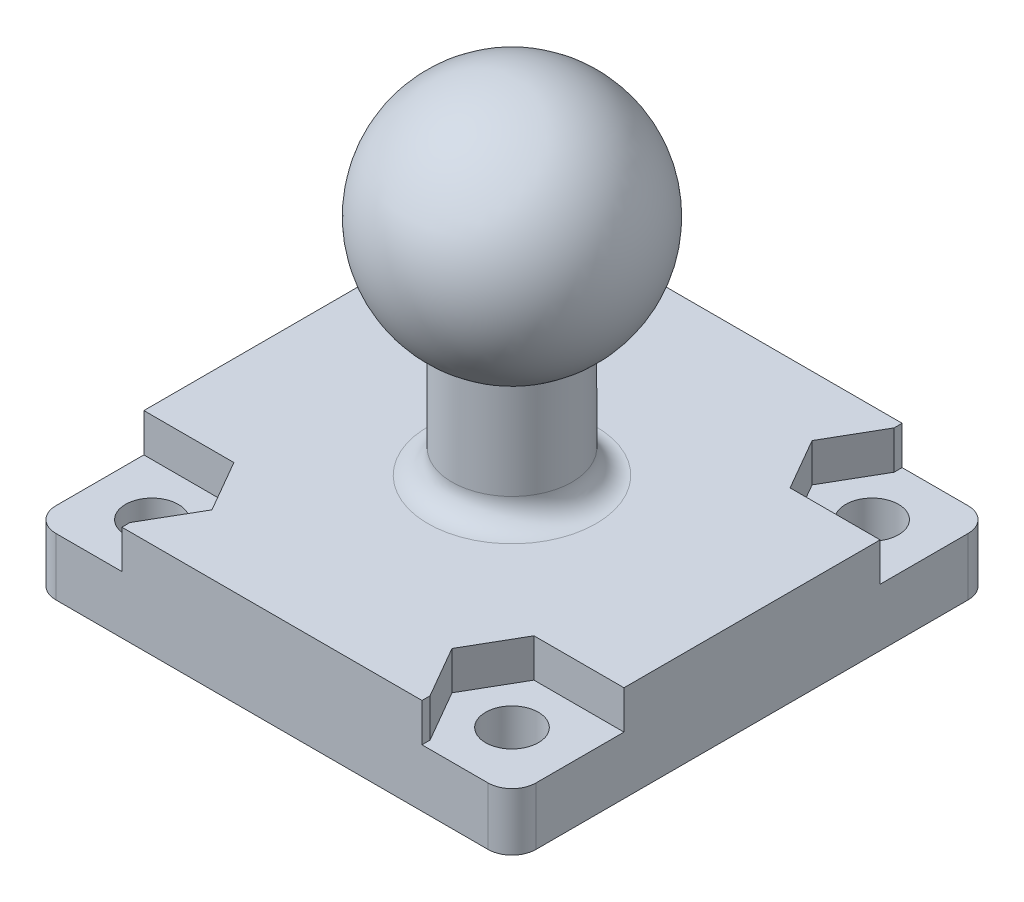
SolidWorks part; units mm, degrees
ref_plane "Plan de face" through (0, 0, 0) normal (0, 0, 1) x (1, 0, 0)
ref_plane "Plan de dessus" through (0, 0, 0) normal (0, 1, 0) x (1, 0, 0)
ref_plane "Plan de droite" through (0, 0, 0) normal (1, 0, 0) x (0, 0, -1)
sketch "Esquisse1" plane through (0, 0, 0) normal (0, 0, 1) x (1, 0, 0)
  line L0 (-2.5, -4.3301) -> (-2.5, -9.3301)
  line L1 (-2.5, -9.3301) -> (0, -9.3301)
  line L2 (0, -9.3301) -> (0, 5)
  line L3 (0, 5) -> (-7.2649, 5) construction
  arc A0 (0, 5) -> (-2.5, -4.3301) centre (0, 0) ccw
  dimension "D1" = 5
  dimension "D2" = 5
  dimension "D3" = 2.5
revolve "Révolution1" add sketch "Esquisse1" angle 360 about L2
sketch "Esquisse2" plane through (0, -9.3301, 0) normal (0, -1, 0) x (1, 0, 0)
  line L1 (-10, 10) -> (10, 10)
  line L2 (-10, 10) -> (-10, -10)
  line L3 (-10, -10) -> (10, -10)
  line L4 (10, 10) -> (10, -10)
  circle A0 centre (0, 0) radius 2.5 construction
  dimension "D3" = 10
  dimension "D4" = 10
  dimension "D1" = 20
  dimension "D2" = 20
extrude "Boss.-Extru.1" add sketch "Esquisse2" along normal blind 4
sketch "Esquisse3" plane through (0, -9.3301, 0) normal (0, 1, 0) x (1, 0, 0)
  circle A0 centre (7.5, -7.5) radius 1.1
  circle A1 centre (7.5, 7.5) radius 1.1
  circle A2 centre (-7.5, 7.5) radius 1.1
  circle A3 centre (-7.5, -7.5) radius 1.1
  circle A4 centre (0, 0) radius 2.5 construction
  dimension "D1" = 2.2
  dimension "D2" = 15
  dimension "D3" = 15
  dimension "D4" = 7.5
  dimension "D5" = 7.5
extrude "Enlèv. mat.-Extru.1" cut sketch "Esquisse3" against normal up to next
fillet "Congé1" radius 1 5 edges at (-10, -11.3301, -10) (2.5, -9.3301, 0) (10, -11.3301, -10) (10, -11.3301, 10) (-10, -11.3301, 10)
sketch "Esquisse4" plane through (0, -9.3301, 0) normal (0, 1, 0) x (1, 0, 0)
  line L1 (-6.25, -5.3349) -> (-8.75, -5.3349) construction
  line L2 (-8.75, -5.3349) -> (-10, -7.5) construction
  line L3 (-10, -7.5) -> (-8.75, -9.6651) construction
  line L4 (-8.75, -9.6651) -> (-6.25, -9.6651) construction
  line L5 (-6.25, -9.6651) -> (-5, -7.5) construction
  line L6 (-5, -7.5) -> (-6.25, -5.3349) construction
  line L7 (10, -7.5) -> (8.75, -5.3349) construction
  line L8 (8.75, -5.3349) -> (6.25, -5.3349) construction
  line L9 (6.25, -5.3349) -> (5, -7.5) construction
  line L10 (5, -7.5) -> (6.25, -9.6651) construction
  line L11 (6.25, -9.6651) -> (8.75, -9.6651) construction
  line L12 (8.75, -9.6651) -> (10, -7.5) construction
  line L13 (8.75, 5.3349) -> (10, 7.5) construction
  line L14 (10, 7.5) -> (8.75, 9.6651) construction
  line L15 (8.75, 9.6651) -> (6.25, 9.6651) construction
  line L16 (6.25, 9.6651) -> (5, 7.5) construction
  line L17 (5, 7.5) -> (6.25, 5.3349) construction
  line L18 (6.25, 5.3349) -> (8.75, 5.3349) construction
  line L19 (-5, 7.5) -> (-6.25, 9.6651) construction
  line L20 (-6.25, 9.6651) -> (-8.75, 9.6651) construction
  line L21 (-8.75, 9.6651) -> (-10, 7.5) construction
  line L22 (-10, 7.5) -> (-8.75, 5.3349) construction
  line L23 (-8.75, 5.3349) -> (-6.25, 5.3349) construction
  line L24 (-6.25, 5.3349) -> (-5, 7.5) construction
  line L25 (-9, 10) -> (9, 10) construction
  line L26 (-10, -9) -> (-10, 9) construction
  line L27 (9, -10) -> (-9, -10) construction
  line L29 (12.7479, 12.7601) -> (12.7479, 5.3349)
  line L30 (12.7479, 5.3349) -> (6.25, 5.3349)
  line L31 (6.25, 5.3349) -> (5, 7.5)
  line L33 (6.25, -13.4814) -> (14.1436, -13.4814)
  line L34 (14.1436, -13.4814) -> (14.1436, -5.3349)
  line L35 (14.1436, -5.3349) -> (6.25, -5.3349)
  line L36 (6.25, -5.3349) -> (5, -7.5)
  line L37 (-14.2374, -5.3349) -> (-6.25, -5.3349)
  line L38 (-6.25, -5.3349) -> (-5, -7.5)
  line L39 (5, -7.5) -> (6.25, -9.6651)
  line L40 (6.25, -9.6651) -> (6.25, -13.4814)
  line L41 (-5, -7.5) -> (-6.25, -9.6651)
  line L42 (-6.25, -9.6651) -> (-6.25, -13.4396)
  line L43 (-6.25, -13.4396) -> (-14.2374, -13.4396)
  line L44 (-14.2374, -13.4396) -> (-14.2374, -5.3349)
  line L45 (5, 7.5) -> (6.25, 9.6651)
  line L46 (6.25, 9.6651) -> (6.25, 12.7601)
  line L47 (6.25, 12.7601) -> (12.7479, 12.7601)
  line L48 (-6.25, 12.7601) -> (-6.25, 9.6651)
  line L49 (-6.25, 9.6651) -> (-5, 7.5)
  line L50 (-5, 7.5) -> (-6.25, 5.3349)
  line L51 (-6.25, 5.3349) -> (-8.75, 5.3349)
  line L52 (-8.75, 5.3349) -> (-15.5259, 5.3349)
  line L53 (-15.5259, 5.3349) -> (-15.5259, 12.7601)
  line L54 (-15.5259, 12.7601) -> (-6.25, 12.7601)
  circle A0 centre (-7.5, -7.5) radius 2.1651 construction
  circle A1 centre (7.5, -7.5) radius 2.1651 construction
  circle A2 centre (7.5, 7.5) radius 2.1651 construction
  circle A3 centre (-7.5, 7.5) radius 2.1651 construction
  dimension "D1" = 2.5
  dimension "D2" = 2.5
  dimension "D3" = 2.5
  dimension "D4" = 2.5
  dimension "D6" = 0.3349
  dimension "D7" = 0
extrude "Enlèv. mat.-Extru.2" cut sketch "Esquisse4" against normal blind 1.6
